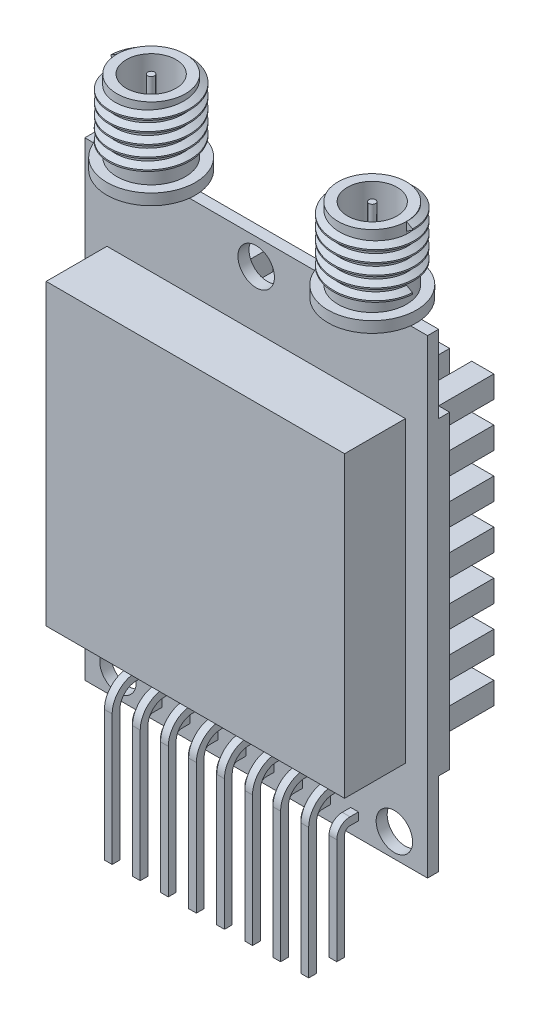
SolidWorks part; units mm, degrees
ref_plane "Спереди" through (0, 0, 0) normal (0, 0, 1) x (1, 0, 0)
ref_plane "Сверху" through (0, 0, 0) normal (0, 1, 0) x (1, 0, 0)
ref_plane "Справа" through (0, 0, 0) normal (1, 0, 0) x (0, 0, -1)
sketch "Эскиз1" plane through (0, 0, 0) normal (0, 0, 1) x (1, 0, 0)
  line L1 (0, 0) -> (31, 0)
  line L2 (0, 0) -> (0, 42.5)
  line L3 (0, 42.5) -> (31, 42.5)
  line L4 (31, 0) -> (31, 42.5)
  dimension "D1" = 31
  dimension "D2" = 42.5
extrude "Бобышка-Вытянуть1" add sketch "Эскиз1" along normal blind 1
sketch "Эскиз2" plane through (0, 0, 1) normal (0, 0, 1) x (1, 0, 0)
  line L0 (31, 42.5) -> (0, 42.5) construction
  line L1 (2, 35) -> (29, 35)
  line L2 (2, 35) -> (2, 8)
  line L3 (2, 8) -> (29, 8)
  line L4 (29, 35) -> (29, 8)
  point P6 (15.5, 35)
  point P7 (15.5, 42.5)
  dimension "D1" = 7.5
  dimension "D2" = 27
  dimension "D3" = 27
extrude "Бобышка-Вытянуть2" add sketch "Эскиз2" along normal blind 5.5
sketch "Эскиз3" plane through (0, 42.5, 0) normal (0, 1, 0) x (1, 0, 0)
  line L0 (15.5, -1) -> (15.5, -6.5) construction
  line L1 (31, -1) -> (0, -1) construction
  line L2 (29, -6.5) -> (2, -6.5) construction
  line L3 (0, -1) -> (0, 0) construction
  circle A0 centre (5.5, -0.5) radius 4
  point P8 (1.5, -0.5)
  point P12 (0, -0.5)
  dimension "D2" = 8
  dimension "D1" = 1.5
extrude "Бобышка-Вытянуть3" add sketch "Эскиз3" along normal blind 1
sketch "Эскиз4" plane through (0, 43.5, 0) normal (0, 1, 0) x (1, 0, 0)
  circle A0 centre (5.5, -0.5) radius 3.1
  dimension "D1" = 6.2
extrude "Бобышка-Вытянуть4" add sketch "Эскиз4" along normal blind 6.5
sketch "Эскиз6" plane through (0, 50, 0) normal (0, 1, 0) x (1, 0, 0)
  circle A0 centre (5.5, -0.5) radius 2.25
  dimension "D1" = 4.5
extrude "Вырез-Вытянуть1" cut sketch "Эскиз6" against normal blind 5
sketch "Эскиз7" plane through (0, 45, 0) normal (0, 1, 0) x (1, 0, 0)
  circle A0 centre (5.5, -0.5) radius 0.3
  dimension "D1" = 0.6
extrude "Бобышка-Вытянуть5" add sketch "Эскиз7" along normal blind 5
ref_plane "Плоскость1" through (15.5, 0, 0) normal (1, 0, 0) x (0, 0, -1)
thread "Резьба1" pitch 1 profile "Профиль резьбы2" start angle 0, offset 0, length 5, pitch 1, diameter 6.2
ref_plane "Плоскость3" through (2.4, 50, 0.5) normal (0, 0, 1) x (-1, 0, 0)
sketch "Профиль резьбы2" plane through (2.4, 50, 0.5) normal (0, 0, 1) x (-1, 0, 0)
  line L0 (0, 0) -> (0, 1) construction
  line L1 (0, 0) -> (0.5413, 0.3125)
  line L2 (0.5413, 0.3125) -> (0.5413, 0.4375)
  line L3 (0.5413, 0.4375) -> (0, 0.75)
  line L4 (0.5413, 0.375) -> (0, 0.375) construction
  line L11 (0, 0) -> (0, 0.75)
  point P2 (0, 0)
  dimension "Pitch" = 1
  dimension "Profile_Angle" = 60
  dimension "Profile_Land" = 0.125
  dimension "Profile_Height" = 0.5413
mirror "Зеркальное отражение1" about plane through (15.5, 0, 0) normal (1, 0, 0) of "Резьба1", "Бобышка-Вытянуть5", "Бобышка-Вытянуть4", "Бобышка-Вытянуть3", "Вырез-Вытянуть1"
sketch "Эскиз8" plane through (31, 0, 0) normal (1, 0, 0) x (0, 0, -1)
  line L0 (-1, 5.3) -> (-3.3, 5.3)
  line L1 (-5.5, 3.1) -> (-5.5, -8.7)
  line L2 (-5.5, -8.7) -> (-4.8, -8.7)
  line L3 (-4.8, -8.7) -> (-4.8, 3.1)
  line L4 (-3.3, 4.6) -> (-1, 4.6)
  line L5 (-1, 4.6) -> (-1, 5.3)
  line L6 (-1, 0) -> (-1, 42.5) construction
  line L7 (-2.96, -8.7) -> (-2.26, -8.7)
  line L8 (-1, 2.06) -> (-1.76, 2.06)
  line L9 (-1, 1.36) -> (-1, 2.06)
  line L10 (-1.76, 1.36) -> (-1, 1.36)
  line L11 (-2.26, -8.7) -> (-2.26, 0.86)
  line L12 (-2.96, -8.7) -> (-2.96, 0.86)
  arc A0 (-4.8, 3.1) -> (-3.3, 4.6) centre (-3.3, 3.1) cw
  arc A1 (-3.3, 5.3) -> (-5.5, 3.1) centre (-3.3, 3.1) ccw
  arc A2 (-2.26, 0.86) -> (-1.76, 1.36) centre (-1.76, 0.86) cw
  arc A3 (-1.76, 2.06) -> (-2.96, 0.86) centre (-1.76, 0.86) ccw
  dimension "D3" = 1.5
  dimension "D4" = 2.2
  dimension "D9" = 0.5
  dimension "D10" = 1.2
  dimension "D1" = 0.7
  dimension "D2" = 0.7
  dimension "D5" = 14
  dimension "D6" = 4.5
  dimension "D7" = 58.7
  dimension "D8" = 0.7
  dimension "D11" = 2.54
  dimension "D12" = 0.7
  dimension "D13" = 2.54
extrude "Бобышка-Вытянуть6" add sketch "Эскиз8" against normal blind 0.7 from offset 6.25 separate body offset against normal yes
pattern_linear "Линейный массив1" count 8 spacing 2.54 along (-1, 0, 0) of "Бобышка-Вытянуть6"
sketch "Эскиз9" plane through (0, 0, 1) normal (0, 0, 1) x (1, 0, 0)
  line L0 (15.5, -3.85) -> (15.5, 3.85) construction
  line L5 (0, 0) -> (31, 0) construction
  line L6 (21.5314, 42.5) -> (9.4686, 42.5) construction
  line L11 (31, 0) -> (31, 42.5) construction
  circle A1 centre (15.5, 40.15) radius 1.65
  circle A2 centre (28, 2.15) radius 1.65
  circle A3 centre (3, 2.15) radius 1.65
  point P0 (3, 0.5)
  point P11 (15.5, 41.8)
  point P12 (15.5, 42.5)
  dimension "D1" = 3.3
  dimension "D3" = 0.5
  dimension "D2" = 38
  dimension "D4" = 25
  dimension "D5" = 3
  dimension "D6" = 0.7
extrude "Вырез-Вытянуть2" cut sketch "Эскиз9" against normal through all
sketch "Эскиз10" plane through (0, 0, 0) normal (0, 0, -1) x (-1, 0, 0)
  line L0 (-31, 0) -> (-31, 42.5) construction
  line L1 (-31, 35.5) -> (0, 35.5)
  line L2 (-31, 35.5) -> (-31, 7.5)
  line L3 (-31, 7.5) -> (0, 7.5)
  line L4 (0, 35.5) -> (0, 7.5)
  line L5 (0, 42.5) -> (0, 0) construction
  line L6 (-21.5314, 42.5) -> (-9.4686, 42.5) construction
  dimension "D1" = 28
  dimension "D2" = 7
extrude "Бобышка-Вытянуть7" add sketch "Эскиз10" along normal blind 6
sketch "Эскиз11" plane through (0, 0, 0) normal (-1, 0, 0) x (0, 0, 1)
  line L0 (-6, 7.5) -> (-6, 35.5) construction
  line L1 (-6, 33.5) -> (-1, 33.5)
  line L2 (-6, 33.5) -> (-6, 31.5)
  line L3 (-6, 31.5) -> (-1, 31.5)
  line L4 (-1, 33.5) -> (-1, 31.5)
  line L5 (-6, 35.5) -> (0, 35.5) construction
  line L6 (-1, 29.5) -> (-1, 27.5)
  line L7 (-6, 29.5) -> (-1, 29.5)
  line L8 (-6, 27.5) -> (-1, 27.5)
  line L9 (-6, 29.5) -> (-6, 27.5)
  line L10 (-1, 25.5) -> (-1, 23.5)
  line L11 (-6, 25.5) -> (-1, 25.5)
  line L12 (-6, 23.5) -> (-1, 23.5)
  line L13 (-6, 25.5) -> (-6, 23.5)
  line L14 (-1, 21.5) -> (-1, 19.5)
  line L15 (-6, 21.5) -> (-1, 21.5)
  line L16 (-6, 19.5) -> (-1, 19.5)
  line L17 (-6, 21.5) -> (-6, 19.5)
  line L18 (-1, 17.5) -> (-1, 15.5)
  line L19 (-6, 17.5) -> (-1, 17.5)
  line L20 (-6, 15.5) -> (-1, 15.5)
  line L21 (-6, 17.5) -> (-6, 15.5)
  line L22 (-1, 13.5) -> (-1, 11.5)
  line L23 (-6, 13.5) -> (-1, 13.5)
  line L24 (-6, 11.5) -> (-1, 11.5)
  line L25 (-6, 13.5) -> (-6, 11.5)
  line L26 (-1, 9.5) -> (-1, 7.5)
  line L27 (-6, 9.5) -> (-1, 9.5)
  line L28 (-6, 7.5) -> (-1, 7.5)
  line L29 (-6, 9.5) -> (-6, 7.5)
  point P8 (-1, 32.5)
  point P9 (-6, 32.5)
  dimension "D1" = 2
  dimension "D2" = 2
  dimension "D3" = 5
  dimension "D4" = 7
extrude "Вырез-Вытянуть3" cut sketch "Эскиз11" against normal through all
sketch "Эскиз12" plane through (0, 9.5, 0) normal (0, -1, 0) x (1, 0, 0)
  line L0 (31, -6) -> (0, -6) construction
  line L1 (2, -6) -> (4, -6)
  line L2 (2, -6) -> (2, -1)
  line L3 (2, -1) -> (4, -1)
  line L4 (4, -6) -> (4, -1)
  line L5 (31, -1) -> (0, -1) construction
  line L6 (0, -1) -> (0, -6) construction
  line L7 (6, -6) -> (6, -1)
  line L8 (6, -1) -> (8, -1)
  line L9 (8, -6) -> (8, -1)
  line L10 (6, -6) -> (8, -6)
  line L11 (10, -6) -> (10, -1)
  line L12 (10, -1) -> (12, -1)
  line L13 (12, -6) -> (12, -1)
  line L14 (10, -6) -> (12, -6)
  line L15 (14, -6) -> (14, -1)
  line L16 (14, -1) -> (16, -1)
  line L17 (16, -6) -> (16, -1)
  line L18 (14, -6) -> (16, -6)
  line L19 (18, -6) -> (18, -1)
  line L20 (18, -1) -> (20, -1)
  line L21 (20, -6) -> (20, -1)
  line L22 (18, -6) -> (20, -6)
  line L23 (22, -6) -> (22, -1)
  line L24 (22, -1) -> (24, -1)
  line L25 (24, -6) -> (24, -1)
  line L26 (22, -6) -> (24, -6)
  line L27 (26, -6) -> (26, -1)
  line L28 (26, -1) -> (28, -1)
  line L29 (28, -6) -> (28, -1)
  line L30 (26, -6) -> (28, -6)
  line L31 (30, -6) -> (30, -1)
  line L32 (30, -1) -> (32, -1)
  line L33 (32, -6) -> (32, -1)
  line L34 (30, -6) -> (32, -6)
  dimension "D1" = 2
  dimension "D2" = 2
  dimension "D3" = 8
extrude "Вырез-Вытянуть4" cut sketch "Эскиз12" against normal up to surface (26 mm away) up to face at (15.5, 35.5, -3)
